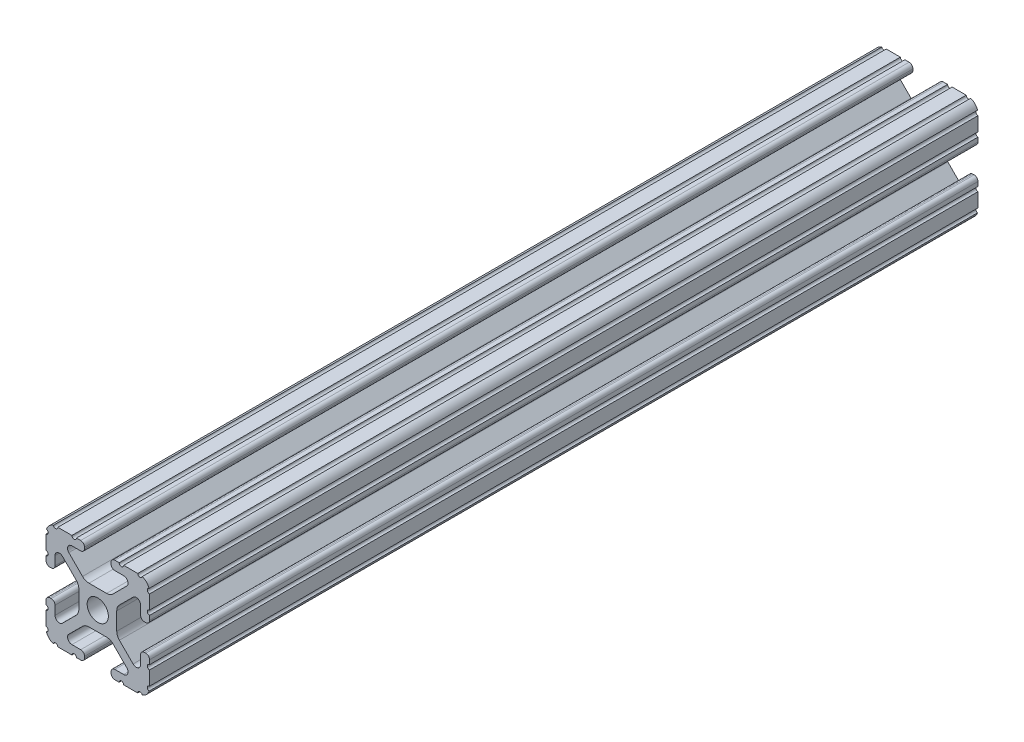
SolidWorks part; units mm, degrees
material "6061-T6 (SS)"
ref_plane "Front Plane" through (0, 0, 0) normal (0, 0, 1) x (1, 0, 0)
ref_plane "Top Plane" through (0, 0, 0) normal (0, 1, 0) x (1, 0, 0)
ref_plane "Right Plane" through (0, 0, 0) normal (1, 0, 0) x (0, 0, -1)
sketch "Sketch2" plane through (0, 0, 0) normal (0, 0, 1) x (1, 0, 0)
  line L0 (0, 12.7) -> (0, -12.7) construction
  line L1 (-12.7, 0) -> (12.7, 0) construction
  line L2 (3.2512, -12.7) -> (12.7, -12.7)
  line L3 (12.7, -12.7) -> (12.7, -3.2512)
  line L4 (3.2512, -12.7) -> (3.2512, -10.4902)
  line L5 (3.2512, -10.4902) -> (8.9276, -10.4902)
  line L6 (8.9276, -10.4902) -> (3.0856, -4.6482)
  line L7 (0, 0) -> (12.7, -12.7) construction
  line L8 (12.7, -3.2512) -> (10.4902, -3.2512)
  line L9 (10.4902, -3.2512) -> (10.4902, -8.9276)
  line L10 (10.4902, -8.9276) -> (4.6482, -3.0856)
  circle A0 centre (0, 0) radius 2.6035
  arc A1 (6.3485, -10.4902) -> (7.1039, -8.6665) centre (6.3485, -9.4219) ccw construction
  point P8 (0, -4.6482)
  dimension "Center Hole Diameter" = 5.207
  dimension "Rail Height" = 25.4
  dimension "Rail Width" = 25.4
  dimension "T-Slot Width" = 6.5024
  dimension "Slot Inner Width" = 14.8336
  dimension "Thickness" = 2.2098
  dimension "Slot Depth" = 5.842
  dimension "D1" = 2.2098
sketch "Sketch3" plane through (0, 0, 0) normal (1, 0, 0) x (0, 0, -1)
  line L0 (-101.6, -12.7) -> (101.6, -12.7) construction
  line L1 (-91.44, 0) -> (91.44, 0) construction
  dimension "Length" = 203.2
  dimension "D1" = 182.88
sketch "Sketch4" plane through (0, 0, 0) normal (0, 0, 1) x (1, 0, 0)
  line L0 (4.1904, -12.7) -> (10.1173, -12.7)
  line L1 (3.2512, -12.7) -> (12.7, -12.7) construction
  line L2 (3.2512, -12.7) -> (3.2512, -10.4902) construction
  line L3 (3.2512, -10.4902) -> (8.9276, -10.4902) construction
  line L4 (3.2512, -11.4294) -> (3.2512, -11.7608)
  line L5 (4.1904, -10.4902) -> (6.3485, -10.4902)
  line L6 (0, -4.6482) -> (2.164, -4.6482)
  line L7 (8.9276, -10.4902) -> (3.0856, -4.6482) construction
  line L8 (3.7373, -5.2999) -> (7.1039, -8.6665)
  line L9 (12.7, -12.7) -> (12.7, -3.2512) construction
  line L10 (10.4902, -8.9276) -> (4.6482, -3.0856) construction
  line L11 (10.4902, -3.2512) -> (10.4902, -8.9276) construction
  line L12 (10.4902, -6.3485) -> (10.4902, -4.1904)
  line L13 (12.7, -3.2512) -> (10.4902, -3.2512) construction
  line L14 (11.4294, -3.2512) -> (11.7608, -3.2512)
  line L15 (12.7, -4.1904) -> (12.7, -10.1173)
  line L16 (8.6665, -7.1039) -> (5.2999, -3.7373)
  line L17 (4.6482, 0) -> (4.6482, -2.164)
  line L18 (-12.7, 0) -> (12.7, 0) construction
  line L19 (0, -4.6482) -> (0, -2.6035)
  line L20 (0, 12.7) -> (0, -12.7) construction
  line L21 (4.6482, 0) -> (2.6035, 0)
  arc A0 (3.2512, -11.7608) -> (4.1904, -12.7) centre (4.1904, -11.7608) ccw
  arc A2 (3.2512, -11.4294) -> (4.1904, -10.4902) centre (4.1904, -11.4294) cw
  arc A3 (6.3485, -10.4902) -> (7.1039, -8.6665) centre (6.3485, -9.4219) ccw
  arc A4 (2.164, -4.6482) -> (3.7373, -5.2999) centre (2.164, -6.8732) cw
  arc A5 (10.1173, -12.7) -> (12.7, -10.1173) centre (10.1173, -10.1173) ccw
  arc A6 (8.6665, -7.1039) -> (10.4902, -6.3485) centre (9.4219, -6.3485) ccw
  arc A7 (10.4902, -4.1904) -> (11.4294, -3.2512) centre (11.4294, -4.1904) cw
  arc A8 (11.7608, -3.2512) -> (12.7, -4.1904) centre (11.7608, -4.1904) cw
  arc A9 (5.2999, -3.7373) -> (4.6482, -2.164) centre (6.8732, -2.164) cw
  circle A10 centre (0, 0) radius 2.6035 construction
  arc A11 (0, -2.6035) -> (2.6035, 0) centre (0, 0) ccw
  dimension "D1" = 2.5827
  dimension "D2" = 2.225
  dimension "D3" = 0.9392
extrude "Boss-Extrude1" add sketch "Sketch4" along normal mid plane 203.2
sketch "Sketch5" plane through (0, 0, 0) normal (0, 0, 1) x (1, 0, 0)
  line L0 (3.2512, -12.7) -> (12.7, -12.7) construction
  line L1 (4.1904, -10.4902) -> (6.3485, -10.4902) construction
  line L3 (0, 0) -> (12.7, -12.7) construction
  line L4 (6.3485, -10.4902) -> (6.3485, -12.7) construction
  line L5 (8.9276, -10.4902) -> (3.0856, -4.6482) construction
  circle A0 centre (10.3562, -12.7) radius 0.5524
  circle A1 centre (5.796, -12.7) radius 0.5524
  circle A2 centre (12.7, -10.3562) radius 0.5524
  circle A3 centre (12.7, -5.796) radius 0.5524
  point P10 (5.2694, -10.4902)
  point P12 (9.4219, -6.3485)
  dimension "D1" = 1.1049
extrude "Cut-Extrude1" cut sketch "Sketch5" against normal through all both and the other way through all
mirror "Mirror1" about plane through (0, 0, 0) normal (1, 0, 0) of bodies 137 134
mirror "Mirror2" about plane through (0, 0, 0) normal (0, 1, 0) of bodies 135
equation "\"D1@Boss-Extrude1\"=\"Length@Sketch3\""
equation "\"D1@Sketch2\"=\"Thickness@Sketch2\""
equation "\"D2@Sketch4\"=\"Slot Inner Width@Sketch2\"*0.15"
equation "\"D1@Sketch4\"=\"D3@Sketch4\"*2.75"
equation "\"D3@Sketch4\"=\"Thickness@Sketch2\"*0.425"
equation "\"D1@Sketch5\"=\"Thickness@Sketch2\"*0.5"
equation "\"D1@Sketch3\"=\"Length@Sketch3\"*0.9"
